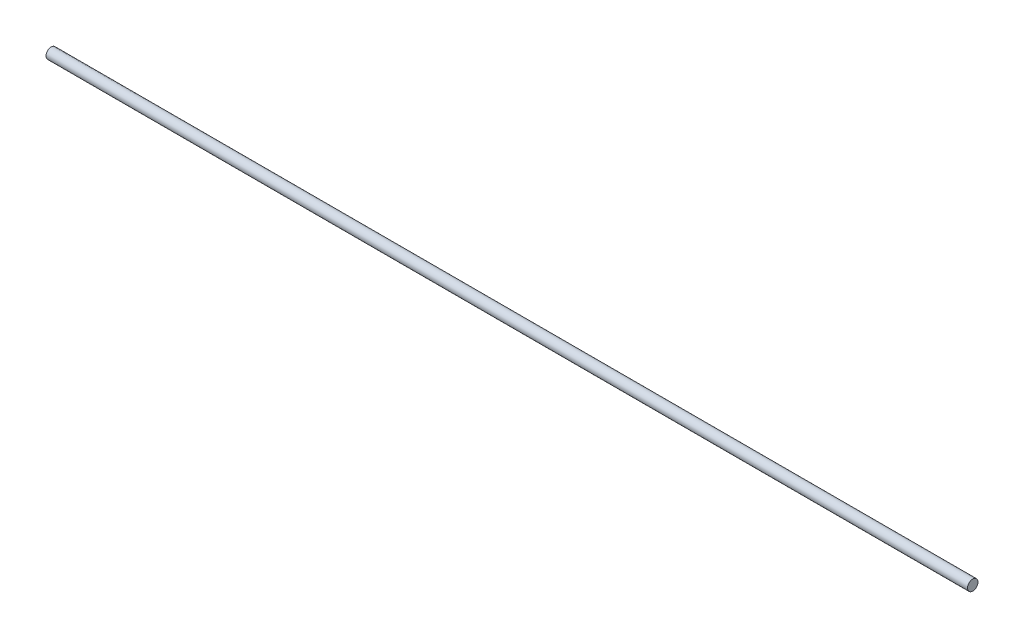
SolidWorks part; units mm, degrees
ref_plane "Front Plane" through (0, 0, 0) normal (0, 0, 1) x (1, 0, 0)
ref_plane "Top Plane" through (0, 0, 0) normal (0, 1, 0) x (1, 0, 0)
ref_plane "Right Plane" through (0, 0, 0) normal (1, 0, 0) x (0, 0, -1)
sketch "Sketch1" plane through (0, 0, 0) normal (1, 0, 0) x (0, 0, -1)
  circle A0 centre (0, 0) radius 5
  dimension "D1" = 10
extrude "Boss-Extrude1" add sketch "Sketch1" along normal blind 880
